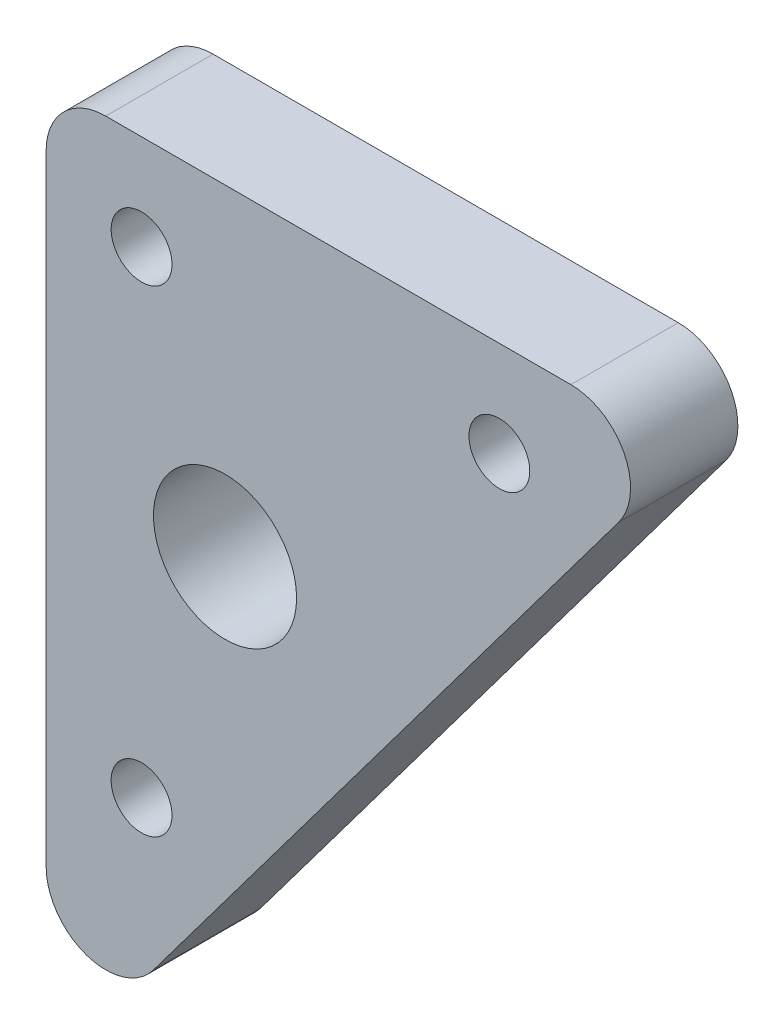
SolidWorks part; units mm, degrees
ref_plane "前视基准面" through (0, 0, 0) normal (0, 0, 1) x (1, 0, 0)
ref_plane "上视基准面" through (0, 0, 0) normal (0, 1, 0) x (1, 0, 0)
ref_plane "右视基准面" through (0, 0, 0) normal (1, 0, 0) x (0, 0, -1)
sketch "草图1" plane through (0, 0, 0) normal (0, 0, 1) x (1, 0, 0)
  line L0 (-11.7284, 12.1605) -> (-11.7284, -27.8395) construction
  line L1 (-11.7284, -27.8395) -> (18.2716, 12.1605) construction
  line L2 (18.2716, 12.1605) -> (-11.7284, 12.1605) construction
  line L3 (-19.7284, 20.1605) -> (34.2716, 20.1605)
  line L4 (34.2716, 20.1605) -> (-19.7284, -51.8395)
  line L5 (-19.7284, -51.8395) -> (-19.7284, 20.1605)
  circle A0 centre (-11.7284, 12.1605) radius 2.55
  circle A1 centre (18.2716, 12.1605) radius 2.55
  circle A2 centre (-11.7284, -27.8395) radius 2.55
  circle A3 centre (-4.7284, -6.8395) radius 6
  dimension "D3" = 5.1
  dimension "D7" = 12
  dimension "D9" = 15
  dimension "D1" = 30
  dimension "D2" = 40
  dimension "D4" = 8
  dimension "D5" = 8
  dimension "D6" = 8
  dimension "D8" = 15
extrude "凸台-拉伸1" add sketch "草图1" along normal blind 9
fillet "圆角1" radius 5 3 edges at (-19.7284, -51.8395, 4.5) (34.2716, 20.1605, 4.5) (-19.7284, 20.1605, 4.5)
